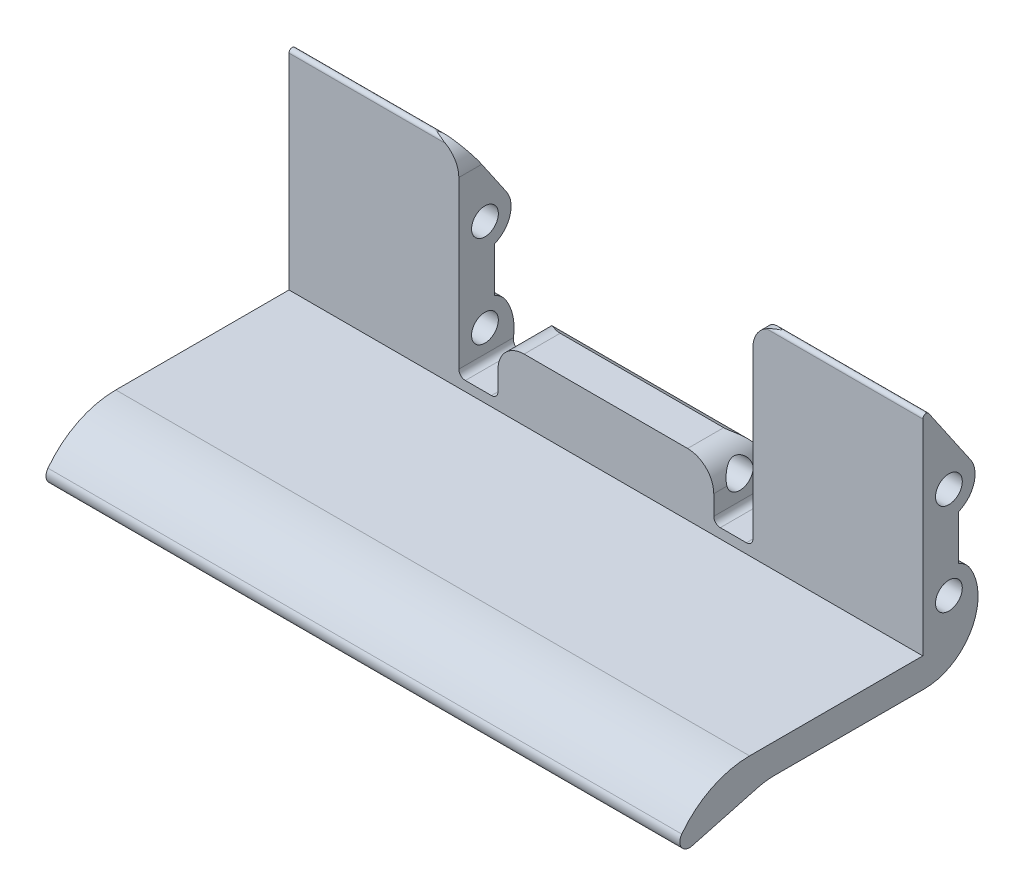
SolidWorks part; units mm, degrees
ref_plane "Front Plane" through (0, 0, 0) normal (0, 0, 1) x (1, 0, 0)
ref_plane "Top Plane" through (0, 0, 0) normal (0, 1, 0) x (1, 0, 0)
ref_plane "Right Plane" through (0, 0, 0) normal (1, 0, 0) x (0, 0, -1)
sketch "Sketch2" plane through (0, 0, 0) normal (1, 0, 0) x (0, 0, -1)
  line L17 (4, 9.4071) -> (4, 30.0493) construction
  line L22 (-26.5127, 4.5) -> (-3, 4.5)
  line L24 (0.265, 0) -> (-22.6845, 0)
  line L26 (0, 35.905) -> (0, 7.5)
  line L27 (5.5, 14.0063) -> (5.5, 20.8919)
  line L28 (0.9125, 36.1875) -> (7.3003, 26.8601)
  line L36 (4, 10.5) -> (10.4174, -13.45) construction
  line L37 (5.4007, 4.7723) -> (-61.2652, -13.0907) construction
  line L38 (-25.2726, -0.3407) -> (-35.3105, -3.0304)
  line L39 (-36.6998, -3.1058) -> (-35.8491, -6.2805) construction
  line L41 (0, 7.5) -> (0, 4.5)
  line L42 (0, 4.5) -> (-3, 4.5)
  circle A12 centre (4, 24.6) radius 2.05
  circle A13 centre (4, 10.5) radius 2.05
  arc A14 (5.5, 20.8919) -> (7.3003, 26.8601) centre (4, 24.6) ccw
  arc A15 (7.2473, 12.4997) -> (5.5, 14.0063) centre (4, 10.5) ccw
  arc A16 (0, 35.905) -> (0.9125, 36.1875) centre (0.5, 35.905) cw
  arc A20 (7.2473, 12.4997) -> (5.5, 14.0063) centre (4, 10.5) ccw
  arc A22 (-36.8969, -0.6791) -> (-26.5127, 4.5) centre (-26.5127, -8.5) cw
  arc A23 (0.265, 0) -> (7.2473, 12.4997) centre (0.265, 8.2) ccw
  arc A24 (-22.6845, 0) -> (-25.2726, -0.3407) centre (-22.6845, -10) ccw
  arc A25 (-36.8969, -0.6791) -> (-35.3105, -3.0304) centre (-35.6988, -1.5815) ccw
  point P12 (0, 37.52)
  point P20 (-35.8491, -1.5815)
  point P24 (-24.001, 0)
  point P25 (5.5529, 4.7044)
  dimension "D3" = 33.02
  dimension "D6" = 1.5
  dimension "D7" = 0.5
  dimension "D9" = 4.5
  dimension "D5" = 8
  dimension "D2" = 6
  dimension "D1" = 4.1
  dimension "D10" = 10
  dimension "D11" = 1.5
  dimension "D16" = 13
  dimension "D4" = 14.1
  dimension "D8" = 3
  dimension "D12" = 15
  dimension "D13" = 6
extrude "Boss-Extrude1" add sketch "Sketch2" along normal blind 97.028
ref_plane "Plane1" through (0, 0, 10) normal (0, 0, 1) x (1, 0, 0)
sketch "Sketch4" plane through (0, 0, 10) normal (0, 0, 1) x (1, 0, 0)
  line L0 (0, 4.5) -> (97.028, 4.5) construction
  line L1 (26, 7) -> (26, 32.405)
  line L2 (97.028, 36.405) -> (0, 36.405) construction
  line L3 (0, 35.905) -> (0, 4.5) construction
  line L4 (48.514, 4.5) -> (48.514, 36.405) construction
  line L5 (32, 7) -> (32, 10)
  line L6 (27, 6) -> (31, 6)
  line L7 (36, 14) -> (61.028, 14)
  line L8 (22, 36.405) -> (75.028, 36.405)
  line L9 (70.028, 6) -> (66.028, 6)
  line L10 (65.028, 7) -> (65.028, 10)
  line L11 (71.028, 7) -> (71.028, 32.405)
  arc A0 (31, 6) -> (32, 7) centre (31, 7) ccw
  arc A1 (27, 6) -> (26, 7) centre (27, 7) cw
  arc A2 (32, 10) -> (36, 14) centre (36, 10) cw
  arc A3 (26, 32.405) -> (22, 36.405) centre (22, 32.405) ccw
  arc A4 (71.028, 32.405) -> (75.028, 36.405) centre (75.028, 32.405) cw
  arc A5 (65.028, 10) -> (61.028, 14) centre (61.028, 10) ccw
  arc A6 (70.028, 6) -> (71.028, 7) centre (70.028, 7) ccw
  arc A7 (66.028, 6) -> (65.028, 7) centre (66.028, 7) cw
  point P19 (71.028, 36.405)
  point P25 (26, 36.405)
  point P26 (48.514, 14)
  point P35 (48.514, 36.405)
  dimension "D3" = 1
  dimension "D5" = 4
  dimension "D6" = 4
  dimension "D1" = 26
  dimension "D2" = 6
  dimension "D4" = 1.5
  dimension "D7" = 19
extrude "Cut-Extrude2" cut sketch "Sketch4" against normal through all
